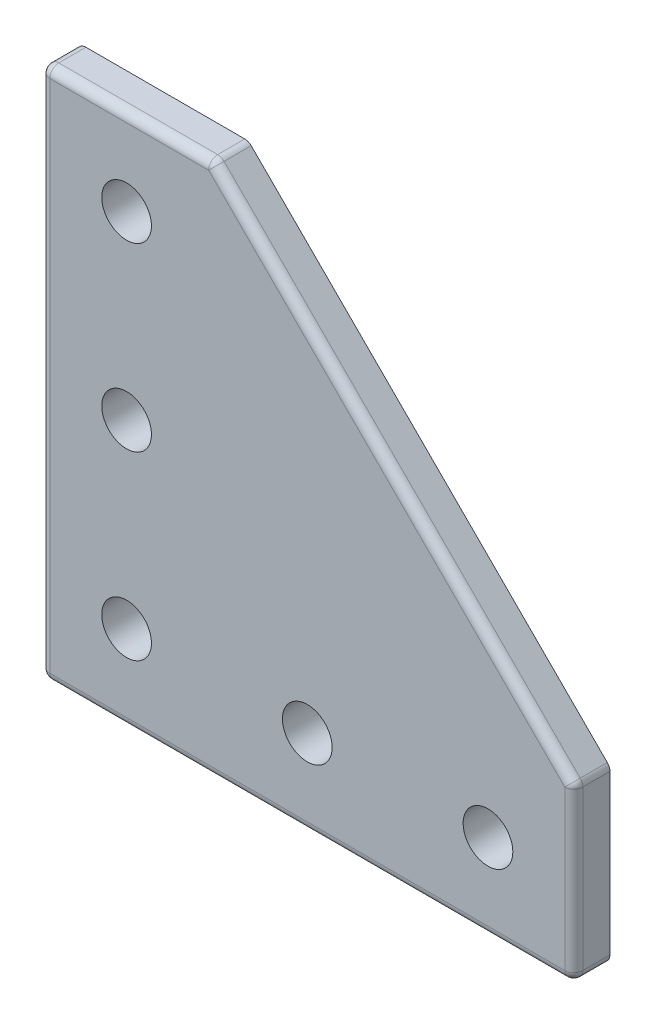
SolidWorks part; units mm, degrees
ref_plane "Front Plane" through (0, 0, 0) normal (0, 0, 1) x (1, 0, 0)
ref_plane "Top Plane" through (0, 0, 0) normal (0, 1, 0) x (1, 0, 0)
ref_plane "Right Plane" through (0, 0, 0) normal (1, 0, 0) x (0, 0, -1)
sketch "Sketch1" plane through (0, 0, 0) normal (0, 0, 1) x (1, 0, 0)
  line L0 (0, 0) -> (0, 59)
  line L1 (9.5, 9.5) -> (29.5, 9.5) construction
  line L2 (29.5, 9.5) -> (49.5, 9.5) construction
  line L3 (9.5, 9.5) -> (9.5, 29.5) construction
  line L4 (19, 59) -> (0, 59)
  line L5 (59, 0) -> (0, 0)
  line L6 (9.5, 29.5) -> (9.5, 49.5) construction
  line L7 (59, 19) -> (59, 0)
  line L8 (19, 59) -> (59, 19)
  line L9 (59, 9.5) -> (49.5, 9.5) construction
  line L10 (9.5, 59) -> (9.5, 49.5) construction
  circle A0 centre (9.5, 9.5) radius 2.75
  circle A1 centre (29.5, 9.5) radius 2.75
  circle A2 centre (49.5, 9.5) radius 2.75
  circle A3 centre (9.5, 29.5) radius 2.75
  circle A4 centre (9.5, 49.5) radius 2.75
  dimension "D1" = 20
  dimension "E" = 5.5
  dimension "D2" = 9.5
  dimension "C" = 59
  dimension "D3" = 20
  dimension "B" = 59
  dimension "D4" = 9.5
extrude "Boss-Extrude1" add sketch "Sketch1" along normal mid plane 4
fillet "Fillet1" radius 1 10 edges at (0, 0, 0) (0, 29.5, 2) (29.5, 0, 2) (59, 9.5, 2) (59, 0, 0) (9.5, 59, 2) (0, 59, 0) (39, 39, 2) (59, 19, 0) (19, 59, 0)
